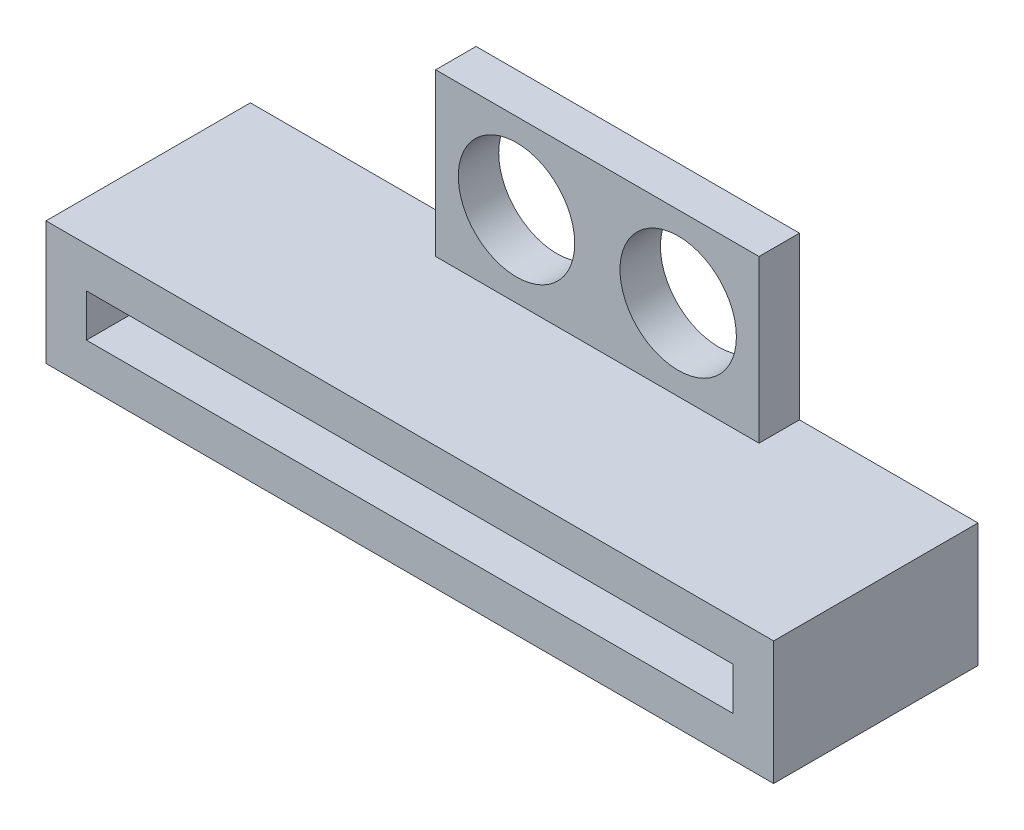
SolidWorks part; units mm, degrees
ref_plane "Front Plane" through (0, 0, 0) normal (0, 0, 1) x (1, 0, 0)
ref_plane "Top Plane" through (0, 0, 0) normal (0, 1, 0) x (1, 0, 0)
ref_plane "Right Plane" through (0, 0, 0) normal (1, 0, 0) x (0, 0, -1)
sketch "Sketch1" plane through (0, 0, 0) normal (0, 0, 1) x (1, 0, 0)
  line L1 (0, 0) -> (25.4, 0)
  line L2 (0, 0) -> (0, -1.6764)
  line L3 (0, -1.6764) -> (25.4, -1.6764)
  line L4 (25.4, 0) -> (25.4, -1.6764)
  line L5 (0, 0) -> (-1.5875, 0)
  line L6 (0, 0) -> (0, 1.5875)
  line L7 (0, 1.5875) -> (-1.5875, 1.5875)
  line L8 (-1.5875, 0) -> (-1.5875, 1.5875)
  line L9 (25.4, -1.6764) -> (26.9875, -1.6764)
  line L10 (25.4, -1.6764) -> (25.4, -3.2639)
  line L11 (25.4, -3.2639) -> (26.9875, -3.2639)
  line L12 (26.9875, -1.6764) -> (26.9875, -3.2639)
  line L13 (-1.5875, 1.5875) -> (26.9875, 1.5875)
  line L14 (-1.5875, 1.5875) -> (-1.5875, -3.2639)
  line L15 (-1.5875, -3.2639) -> (26.9875, -3.2639)
  line L16 (26.9875, 1.5875) -> (26.9875, -3.2639)
extrude "Boss-Extrude1" add sketch "Sketch1" along normal blind 4.8514 contours L16 L13 L6 L1 L4 L9 | L8 L5 L6 L7 | L14 L15 L10 L3 L2 L5 | L12 L9 L10 L11
sketch "Sketch2" plane through (0, 0, 0) normal (0, 0, -1) x (-1, 0, 0)
  line L1 (-26.9875, 1.5875) -> (1.5875, 1.5875)
  line L2 (-26.9875, 1.5875) -> (-26.9875, -3.2639)
  line L3 (-26.9875, -3.2639) -> (1.5875, -3.2639)
  line L4 (1.5875, 1.5875) -> (1.5875, -3.2639)
extrude "Boss-Extrude2" add sketch "Sketch2" along normal blind 3.175
sketch "Sketch3" plane through (0, 1.5875, 0) normal (0, 1, 0) x (1, 0, 0)
  line L0 (12.7, 3.175) -> (13.626, 3.175)
  line L1 (-1.5875, 3.175) -> (26.9875, 3.175) construction
  line L2 (19.976, 3.175) -> (7.276, 3.175)
  line L3 (13.626, 3.175) -> (13.626, 1.5875)
  line L5 (19.976, 3.175) -> (7.276, 3.175)
  line L6 (19.976, 3.175) -> (19.976, 1.5875)
  line L7 (19.976, 1.5875) -> (7.276, 1.5875)
  line L8 (7.276, 3.175) -> (7.276, 1.5875)
  line M4 (26.9875, 3.175) -> (-1.5875, 3.175)
extrude "Boss-Extrude3" add sketch "Sketch3" along normal blind 6.35 contours L7 L6 L3 M4 | L8 L7 L3 M4
sketch "Sketch4" plane through (0, 0, -1.5875) normal (0, 0, 1) x (1, 0, 0)
  line L0 (13.626, 7.9375) -> (13.626, 1.5875)
  line L1 (19.976, 7.9375) -> (7.276, 7.9375) construction
  line L2 (19.976, 1.5875) -> (7.276, 1.5875) construction
  line L3 (13.626, 1.5875) -> (13.626, 4.7625)
  line L4 (13.626, 4.7625) -> (19.976, 4.7625)
  circle A0 centre (16.801, 4.7625) radius 2.286
  circle A1 centre (10.451, 4.7625) radius 2.286
extrude "Cut-Extrude1" cut sketch "Sketch4" against normal blind 6.35 contours L4 A0 | L4 A0 | A1
